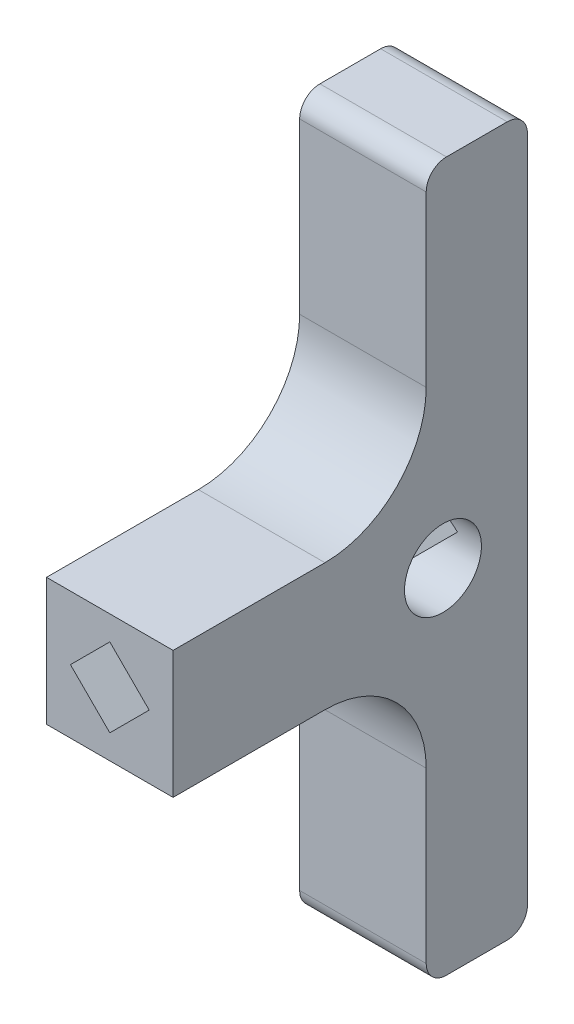
SolidWorks part; units mm, degrees
ref_plane "Plan de face" through (0, 0, 0) normal (0, 0, 1) x (1, 0, 0)
ref_plane "Plan de dessus" through (0, 0, 0) normal (0, 1, 0) x (1, 0, 0)
ref_plane "Plan de droite" through (0, 0, 0) normal (1, 0, 0) x (0, 0, -1)
sketch "Esquisse1" plane through (0, 0, 0) normal (0, 0, 1) x (1, 0, 0)
  line L1 (-6.25, 35) -> (6.25, 35)
  line L2 (-6.25, 35) -> (-6.25, -35)
  line L3 (-6.25, -35) -> (6.25, -35)
  line L4 (6.25, 35) -> (6.25, -35)
  line L5 (-6.25, 35) -> (6.25, -35) construction
  line L6 (-6.25, -35) -> (6.25, 35) construction
  point P0 (0, 0)
  dimension "D1" = 70
  dimension "D2" = 12.5
extrude "Boss.-Extru.1" add sketch "Esquisse1" along normal blind 10
sketch "Esquisse2" plane through (0, 0, 0) normal (0, 0, -1) x (-1, 0, 0)
  line L0 (6.25, 35) -> (6.25, -35) construction
  line L1 (-6.25, 6.2885) -> (6.25, 6.2885)
  line L2 (-6.25, 6.2885) -> (-6.25, -6.2885)
  line L3 (-6.25, -6.2885) -> (6.25, -6.2885)
  line L4 (6.25, 6.2885) -> (6.25, -6.2885)
  line L5 (-6.25, 6.2885) -> (6.25, -6.2885) construction
  line L6 (-6.25, -6.2885) -> (6.25, 6.2885) construction
extrude "Boss.-Extru.2" add sketch "Esquisse2" against normal blind 35
sketch "Esquisse3" plane through (0, 0, 0) normal (0, 0, -1) x (-1, 0, 0)
  line L1 (-3.8891, 0) -> (0, 3.8891)
  line L2 (-3.8891, 0) -> (0, -3.8891)
  line L3 (0, -3.8891) -> (3.8891, 0)
  line L4 (0, 3.8891) -> (3.8891, 0)
  line L5 (-3.8891, 0) -> (3.8891, 0) construction
  line L6 (0, -3.8891) -> (0, 3.8891) construction
  point P0 (0, 0)
  point P6 (0, 0)
  point P7 (0, 0)
  point P8 (0, 0)
  point P9 (0, 0)
  point P10 (3.8891, 0)
  dimension "D1" = 5.5
extrude "Enlèv. mat.-Extru.1" cut sketch "Esquisse3" against normal blind 40
fillet "Congé1" radius 10 2 edges at (0, 6.2885, 10) (0, -6.2885, 10)
fillet "Congé3" radius 2 4 edges at (0, -35, 10) (0, -35, 0) (0, 35, 0) (0, 35, 10)
hole_wizard "Dégagement M71" positions "Esquisse4" profile "Esquisse5" hole size "M7" standard "ISO"
sketch "Esquisse4" plane through (-6.25, 0, 0) normal (-1, 0, 0) x (0, 0, 1)
  point P0 (8.3448, 0)
sketch "Esquisse5" plane through (-6.25, 0, 8.3448) normal (0, 1, 0) x (0, 0, 1)
  line L0 (0, 0) -> (0, 14.7833)
  line L1 (0, 14.7833) -> (3.8, 12.5)
  line L2 (3.8, 12.5) -> (3.8, 0)
  line L5 (3.8, 0) -> (0, 0)
  line L10 (0, 14.7833) -> (-3.8, 12.5) construction
  line L11 (0, -6.35) -> (0, 107.95) construction
  dimension "Diamètre du perçage" = 7.6
  dimension "Profondeur du perçage" = 12.5
  dimension "Angle de pointe" = 118
